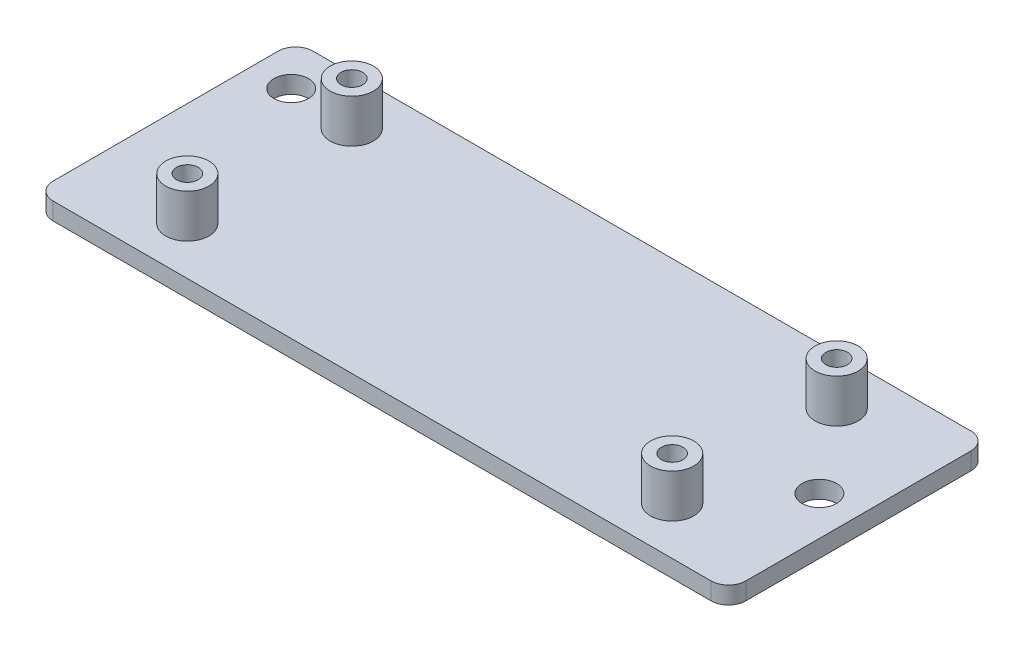
SolidWorks part; units mm, degrees
material "ABS"
ref_plane "Спереди" through (0, 0, 0) normal (0, 0, 1) x (1, 0, 0)
ref_plane "Сверху" through (0, 0, 0) normal (0, 1, 0) x (1, 0, 0)
ref_plane "Справа" through (0, 0, 0) normal (1, 0, 0) x (0, 0, -1)
sketch "Эскиз1" plane through (0, 0, 0) normal (0, 1, 0) x (1, 0, 0)
  line L1 (0, 0) -> (80, 0)
  line L2 (0, 0) -> (0, -30)
  line L3 (0, -30) -> (80, -30)
  line L4 (80, 0) -> (80, -30)
  dimension "D1" = 30
  dimension "D2" = 80
extrude "Бобышка-Вытянуть1" add sketch "Эскиз1" along normal blind 2
sketch "Эскиз2" plane through (0, 2, 0) normal (0, 1, 0) x (1, 0, 0)
  line L0 (0, 0) -> (0, -30) construction
  line L1 (80, 0) -> (0, 0) construction
  line L3 (0, -30) -> (80, -30) construction
  line L4 (80, -30) -> (80, 0) construction
  circle A0 centre (12, -5.5) radius 2.5
  circle A1 centre (12, -24.5) radius 2.5
  circle A2 centre (68, -5.5) radius 2.5
  circle A3 centre (68, -24.5) radius 2.5
  dimension "D1" = 12
  dimension "D2" = 5.5
  dimension "D3" = 12
  dimension "D4" = 5.5
  dimension "D5" = 12
  dimension "D6" = 5.5
  dimension "D7" = 12
  dimension "D8" = 5.5
  dimension "D9" = 5
  dimension "D10" = 5
  dimension "D11" = 5
  dimension "D12" = 5
  dimension "D13" = 56
  dimension "D14" = 19
extrude "Бобышка-Вытянуть2" add sketch "Эскиз2" along normal blind 5
sketch "Эскиз3" plane through (0, 7, 0) normal (0, 1, 0) x (1, 0, 0)
  circle A0 centre (12, -5.5) radius 1.25
  circle A1 centre (12, -24.5) radius 1.25
  circle A2 centre (68, -5.5) radius 1.25
  circle A3 centre (68, -24.5) radius 1.25
  dimension "D1" = 2.5
  dimension "D2" = 2.5
  dimension "D3" = 2.5
  dimension "D4" = 2.5
extrude "Вырез-Вытянуть1" cut sketch "Эскиз3" against normal through all both and the other way through all
sketch "Эскиз4" plane through (0, 2, 0) normal (0, 1, 0) x (1, 0, 0)
  line L0 (0, -15) -> (80, -15) construction
  line L1 (0, 0) -> (0, -30) construction
  line L2 (80, -30) -> (80, 0) construction
  line L3 (80, 0) -> (0, 0) construction
  circle A0 centre (4.5, -5) radius 2
  circle A1 centre (75.5, -15) radius 2
  dimension "D1" = 4.5
  dimension "D2" = 4
  dimension "D3" = 4.5
  dimension "D4" = 4
  dimension "D5" = 5
extrude "Вырез-Вытянуть2" cut sketch "Эскиз4" against normal through all both and the other way through all
fillet "Скругление1" radius 2 1 edges at (0, 1, 30)
fillet "Скругление2" radius 2 1 edges at (0, 1, 0)
fillet "Скругление3" radius 2 1 edges at (80, 1, 0)
fillet "Скругление4" radius 2 1 edges at (80, 1, 30)
